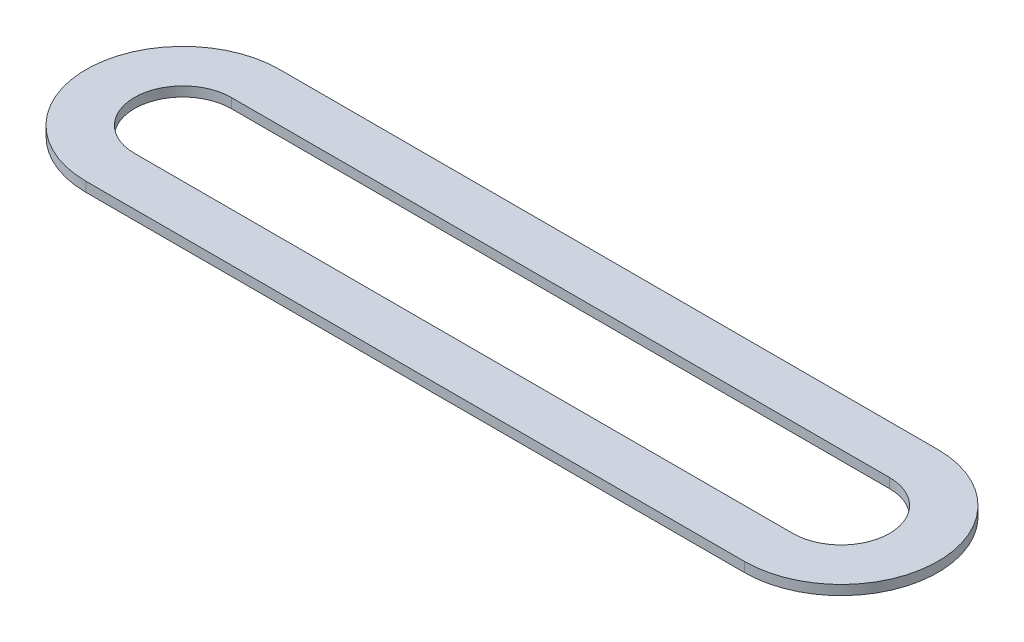
SolidWorks part; units mm, degrees
ref_plane "Front Plane" through (0, 0, 0) normal (0, 0, 1) x (1, 0, 0)
ref_plane "Top Plane" through (0, 0, 0) normal (0, 1, 0) x (1, 0, 0)
ref_plane "Right Plane" through (0, 0, 0) normal (1, 0, 0) x (0, 0, -1)
sketch "Sketch1" plane through (0, 0, 0) normal (0, 1, 0) x (1, 0, 0)
  line L0 (-34, 2.5) -> (0, 2.5)
  line L1 (0, -2.5) -> (-34, -2.5)
  line L2 (-34, 5) -> (0, 5)
  line L3 (-34, -5) -> (0, -5)
  circle A0 centre (-34, 0) radius 2.5
  circle A1 centre (0, 0) radius 2.5
  circle A2 centre (-34, 0) radius 5
  circle A3 centre (0, 0) radius 5
  dimension "D1" = 5
  dimension "D4" = 10
  dimension "D2" = 34
extrude "Boss-Extrude1" add sketch "Sketch1" along normal blind 0.5 contours A2 L1 A0 L0 L2 | A3 L2 A2 L0 | A3 L1 A2 L3 | A3 L0 A1 L1 L3
